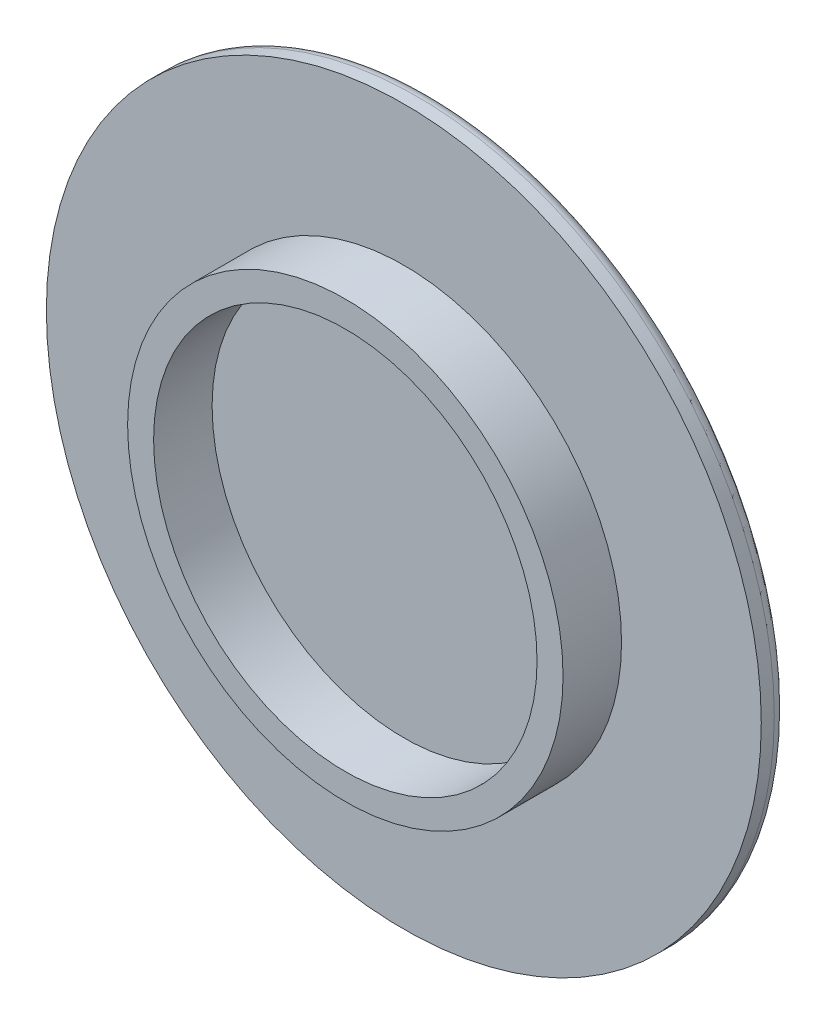
SolidWorks part; units mm, degrees
ref_plane "Alzado" through (0, 0, 0) normal (0, 0, 1) x (1, 0, 0)
ref_plane "Planta" through (0, 0, 0) normal (0, 1, 0) x (1, 0, 0)
ref_plane "Vista lateral" through (0, 0, 0) normal (1, 0, 0) x (0, 0, -1)
sketch "Croquis1" plane through (0, 0, 0) normal (0, 0, 1) x (1, 0, 0)
  circle A0 centre (0, 0) radius 16.75
  circle A1 centre (0, 0) radius 14.75
  dimension "D1" = 33.5
  dimension "D2" = 2
extrude "PestañaEntrada" add sketch "Croquis1" along normal blind 4.5
sketch "Croquis2" plane through (0, 0, 0) normal (0, 0, -1) x (-1, 0, 0)
  circle A0 centre (0, 0) radius 27.5
  dimension "D1" = 55
extrude "Tapadera" add sketch "Croquis2" along normal blind 2
fillet "DetalleSuperior" radius 1 1 edges at (-27.5, 0, -2)
